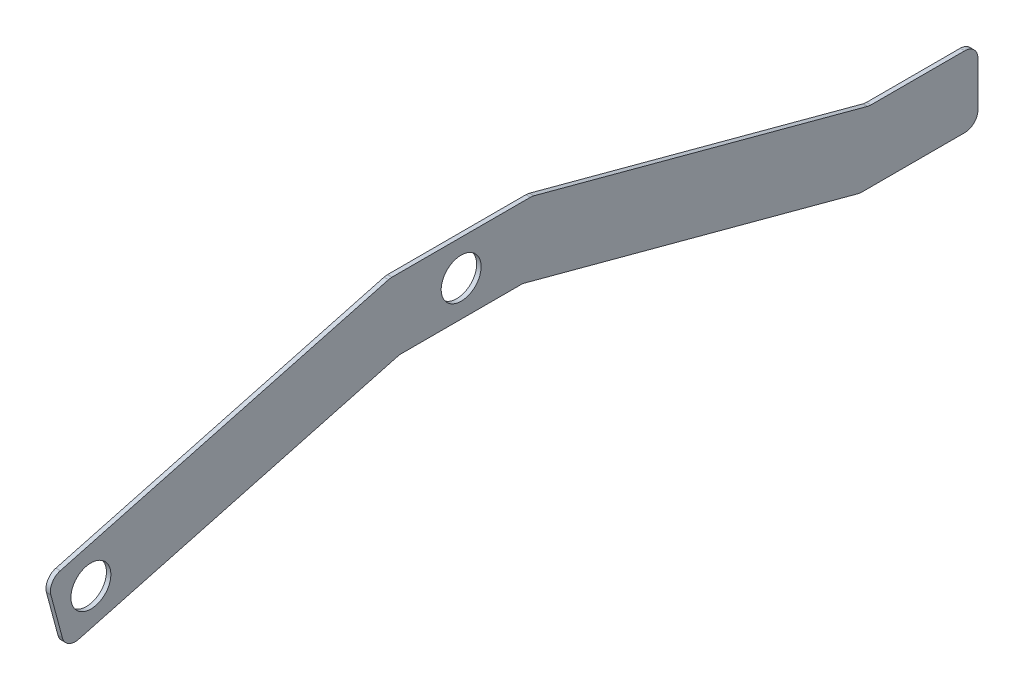
SolidWorks part; units mm, degrees
material "6063-O"
ref_plane "Front" through (0, 0, 0) normal (0, 0, 1) x (1, 0, 0)
ref_plane "Top" through (0, 0, 0) normal (0, 1, 0) x (1, 0, 0)
ref_plane "Right" through (0, 0, 0) normal (1, 0, 0) x (0, 0, -1)
sketch "Sketch1" plane through (0, 0, 0) normal (1, 0, 0) x (0, 0, -1)
  line L0 (-50.8, 25.4) -> (50.8, 25.4)
  line L3 (319.1634, -99.0998) -> (44.1121, -25.4)
  line L4 (44.1121, -25.4) -> (-44.1121, -25.4)
  line L5 (-44.1121, -25.4) -> (-282.9972, -89.4091)
  line L6 (-282.9972, -89.4091) -> (-296.1452, -40.34)
  line L7 (-296.1452, -40.34) -> (-50.8, 25.4)
  line L8 (0, 25.4) -> (0, -25.4) construction
  line L9 (-310.7646, -70.5533) -> (-48606.9507, -13011.4774) construction
  line L13 (601.9041, -58.3005) -> (-49398.0959, -58.3005) construction
  line L14 (-147.7421, -347.18) -> (49852.2579, -347.18) construction
  line L15 (369.9634, -60.1196) -> (369.9634, -337.7005)
  line L16 (369.9634, -337.7005) -> (319.1634, -337.7005)
  line L17 (319.1634, -337.7005) -> (319.1634, -99.0998)
  line L19 (50.8, 25.4) -> (369.9634, -60.1196)
  circle A0 centre (-265.0366, -58.3005) radius 14.2875
  circle A1 centre (0, 0) radius 14.2875
  point P10 (0, 0)
  point P16 (-289.5712, -64.8746)
  point P24 (344.5634, -337.7005)
  dimension "D8" = 28.575
  dimension "D1" = 50.8
  dimension "D2" = 50.8
  dimension "D3" = 609.6
  dimension "D4" = 279.4
  dimension "D5" = 254
  dimension "D6" = 165
  dimension "D7" = 101.6
  dimension "D9" = 25.4
  dimension "D10" = 50.8
  dimension "D11" = 347.18
  dimension "D13" = 50.8
extrude "Boss-Extrude1" add sketch "Sketch1" along normal blind 3.175
sketch "Sketch3" plane through (3.175, 0, 0) normal (1, 0, 0) x (0, 0, -1)
  line L0 (344.5634, -337.7005) -> (344.5634, -53.3137) construction
  line L1 (319.1634, -337.7005) -> (369.9634, -337.7005) construction
  line L2 (369.9634, -60.1196) -> (50.8, 25.4) construction
  circle A0 centre (344.5634, -312.3005) radius 12.7
  dimension "D1" = 25.4
  dimension "D2" = 25.4
extrude "Cut-Extrude2" cut sketch "Sketch3" against normal through all
sketch "Sketch5" plane through (3.175, 0, 0) normal (1, 0, 0) x (0, 0, -1)
  line L0 (369.9634, -337.7005) -> (369.9634, -60.1196) construction
  line L1 (319.1634, -337.7005) -> (369.9634, -337.7005)
  line L2 (319.1634, -337.7005) -> (319.1634, -90.0505)
  line L3 (319.1634, -90.0505) -> (369.9634, -90.0505)
  line L4 (369.9634, -337.7005) -> (369.9634, -90.0505)
  dimension "D1" = 247.65
extrude "Cut-Extrude4" cut sketch "Sketch5" against normal through all
sketch "Sketch6" plane through (3.175, 0, 0) normal (1, 0, 0) x (0, 0, -1)
  line L1 (369.9634, -90.0505) -> (242.9634, -90.0505)
  line L2 (369.9634, -90.0505) -> (369.9634, -115.4505)
  line L3 (369.9634, -115.4505) -> (242.9634, -115.4505)
  line L4 (242.9634, -90.0505) -> (242.9634, -115.4505)
  dimension "D1" = 25.4
  dimension "D2" = 127
extrude "Cut-Extrude5" cut sketch "Sketch6" against normal through all
sketch "Sketch7" plane through (3.175, 0, 0) normal (1, 0, 0) x (0, 0, -1)
  line L0 (292.0791, -39.2505) -> (369.9634, -39.2505)
  line L1 (369.9634, -60.1196) -> (50.8, 25.4) construction
  line L2 (369.9634, -39.2505) -> (369.9634, -60.1196)
  line L3 (369.9634, -90.0505) -> (285.3912, -90.0505) construction
  line L4 (292.0791, -39.2505) -> (369.9634, -60.1196)
  dimension "D1" = 50.8
extrude "Boss-Extrude2" add sketch "Sketch7" against normal blind 3.175
fillet "Fillet1" radius 9.525 10 edges at (1.5875, -39.2505, -369.9634) (1.5875, -90.0505, -369.9634) (1.5875, -90.0505, -285.3912) (1.5875, -39.2505, -292.0791) (1.5875, -25.4, -44.1121) (1.5875, -25.4, 44.1121) (1.5875, 25.4, -50.8) (1.5875, 25.4, 50.8) (1.5875, -89.4091, 282.9972) (1.5875, -40.34, 296.1452)
